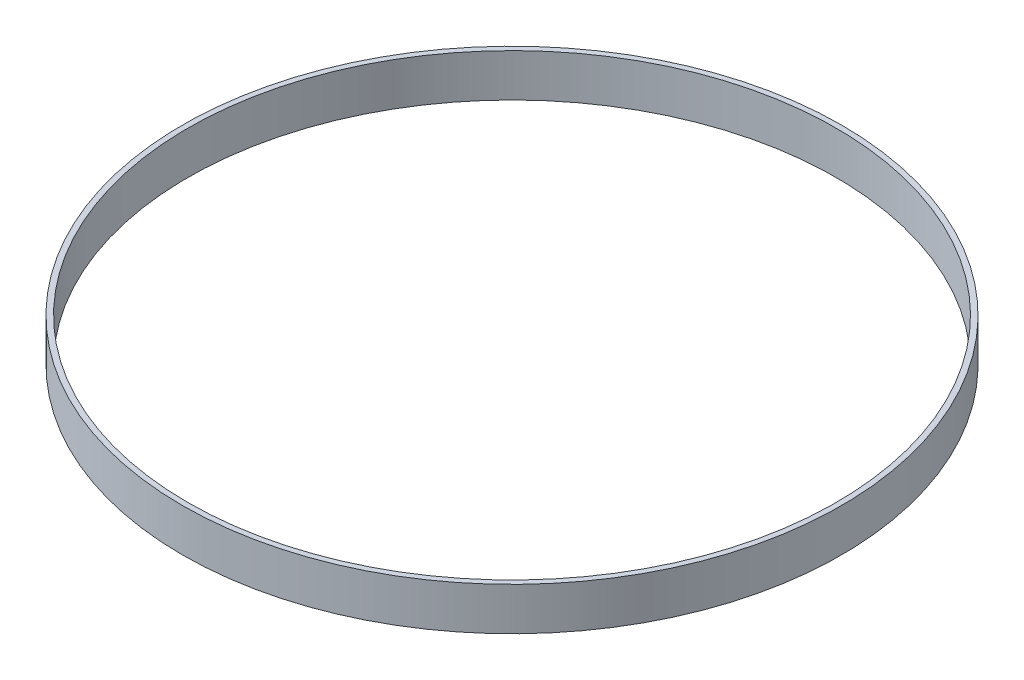
SolidWorks part; units mm, degrees
ref_plane "Front Plane" through (0, 0, 0) normal (0, 0, 1) x (1, 0, 0)
ref_plane "Top Plane" through (0, 0, 0) normal (0, 1, 0) x (1, 0, 0)
ref_plane "Right Plane" through (0, 0, 0) normal (1, 0, 0) x (0, 0, -1)
sketch "Sketch1" plane through (0, 0, 0) normal (0, 1, 0) x (1, 0, 0)
  circle A0 centre (0, 0) radius 96.2025
  circle A1 centre (0, 0) radius 97.79
  dimension "D1" = 195.58
  dimension "D2" = 192.405
extrude "Boss-Extrude1" add sketch "Sketch1" along normal blind 12.7
